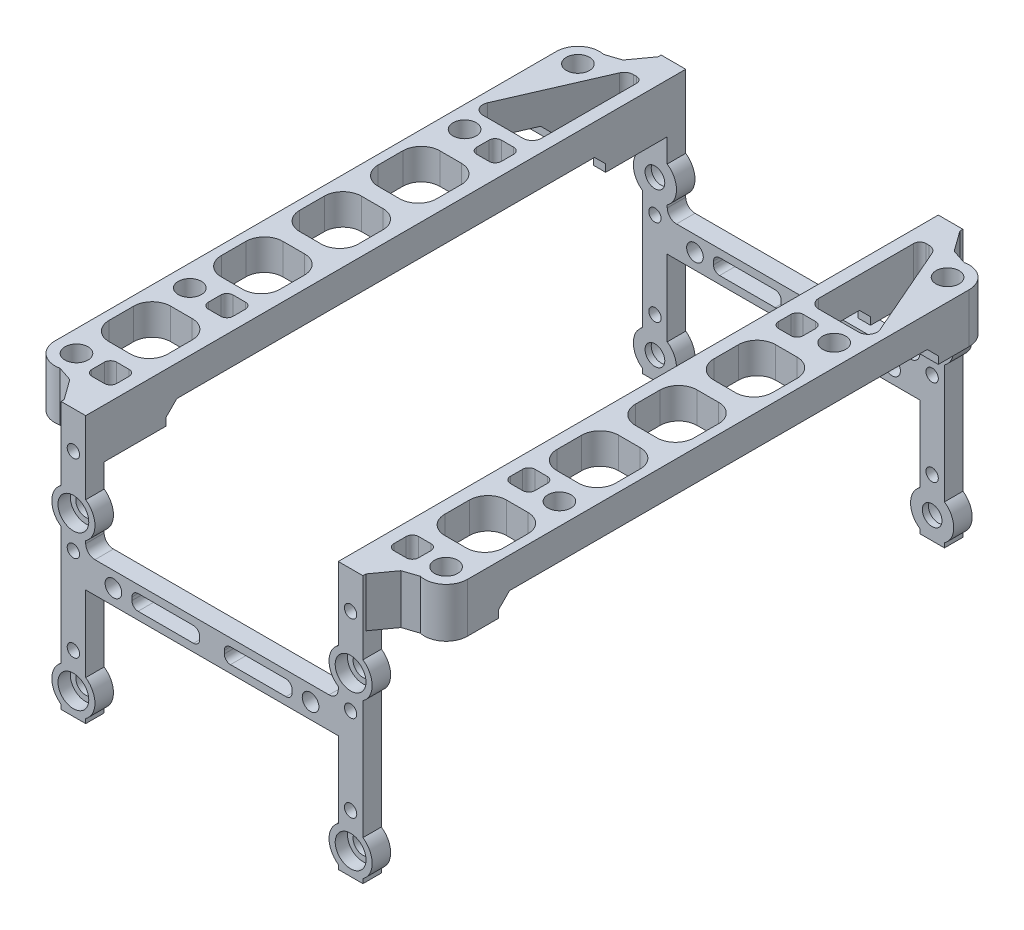
SolidWorks part; units mm, degrees
ref_plane "Front Plane" through (0, 0, 0) normal (0, 0, 1) x (1, 0, 0)
ref_plane "Top Plane" through (0, 0, 0) normal (0, 1, 0) x (1, 0, 0)
ref_plane "Right Plane" through (0, 0, 0) normal (1, 0, 0) x (0, 0, -1)
sketch "Sketch1" plane through (0, 0, 0) normal (1, 0, 0) x (0, 0, -1)
  line L0 (0, 0) -> (-3, 0)
  line L1 (0, 0) -> (91.4, 0) construction
  line L2 (0, 0) -> (0, 35.3)
  line L3 (0, 35.3) -> (91.4, 35.3) construction
  line L4 (91.4, 0) -> (91.4, 35.3)
  line L5 (-3, 0) -> (-3, 43.3)
  line L6 (-3, 43.3) -> (94.4, 43.3) construction
  line L7 (94.4, 43.3) -> (94.4, 0)
  line L8 (94.4, 0) -> (91.4, 0)
  line L9 (45.7, 43.3) -> (45.7, 35.3)
  line L10 (94.4, 43.3) -> (45.7, 43.3)
  line L11 (91.4, 35.3) -> (45.7, 35.3)
  dimension "D1" = 91.4
  dimension "D2" = 35.3
  dimension "D3" = 3
  dimension "D4" = 8
extrude "Boss-Extrude1" add sketch "Sketch1" along normal blind 4 contours L11 L4 L8 L7 L10 L9
sketch "Sketch2" plane through (0, 0, -94.4) normal (0, 0, 1) x (1, 0, 0)
  line L0 (2, 43.3) -> (2, 0) construction
  line L1 (2, 43.3) -> (2, 35.3) construction
  line L4 (4, 43.3) -> (0, 43.3) construction
  line L5 (4, 35.3) -> (0, 35.3) construction
  line L6 (4, 35.3) -> (0, 35.3) construction
  line L7 (4, 0) -> (0, 0) construction
  circle A0 centre (2, 28.6) radius 1.6
  circle A1 centre (2, 3.6) radius 1.6
  circle A3 centre (2, 37.3) radius 1
  circle A4 centre (2, 23.3) radius 1
  circle A5 centre (2, 9.3) radius 1
  dimension "D1" = 3.2
  dimension "D5" = 2
  dimension "D6" = 2
  dimension "D2" = 25
  dimension "D3" = 6.7
  dimension "D4" = 2
  dimension "D7" = 12
  dimension "D8" = 14
extrude "Cut-Extrude1" cut sketch "Sketch2" along normal through all and the other way through all
sketch "Sketch3" plane through (0, 0, -94.4) normal (0, 0, -1) x (-1, 0, 0)
  line L0 (-2, 28.6) -> (43, 28.6) construction
  line L1 (20.5, 28.6) -> (0, 28.6) construction
  line L2 (6, 55.8) -> (20.5, 55.8) construction
  line L5 (20.5, 23.8) -> (20.5, 18.8)
  line L8 (-2, 3.6) -> (42.5, 3.6) construction
  line L9 (20.5, 21.3) -> (0, 21.3) construction
  line L11 (0, 55.8) -> (0, 50.8) construction
  line L12 (20.5, 50.8) -> (6, 50.8) construction
  line L13 (20.5, 55.8) -> (20.5, 50.8) construction
  line L14 (0, 55.8) -> (3, 55.8) construction
  line L15 (0, 53.3) -> (20.5, 53.3) construction
  line L16 (-4, 43.3) -> (-4, 55.8) construction
  line L17 (-4, 55.8) -> (0, 55.8) construction
  line L18 (-4, 43.3) -> (0, 43.3) construction
  line L19 (0, 43.3) -> (0, 50.8) construction
  line L20 (4.5, 53.3) -> (4.5, 21.3) construction
  line L21 (0, 23.8) -> (0, 18.8) construction
  line L22 (0, 43.3) -> (0, 0) construction
  line L23 (-4, 43.3) -> (0, 43.3) construction
  line L24 (-4, 43.3) -> (-4, 0) construction
  line L25 (3, 50.8) -> (0, 50.8) construction
  line L26 (0, 23.8) -> (20.5, 23.8)
  line L27 (20.5, 18.8) -> (0, 18.8)
  line L28 (-4, 43.3) -> (-4, 31.4723) construction
  line L29 (-4, 18.8) -> (0, 18.8)
  line L30 (0, 43.3) -> (0, 35.3)
  line L31 (0, 25.7277) -> (0, 23.8)
  line L32 (-4, 25.7277) -> (-4, 18.8)
  line L34 (8.5, 22.55) -> (17.5, 22.55)
  line L35 (7.5, 21.55) -> (7.5, 21.05)
  line L36 (8.5, 20.05) -> (17.5, 20.05)
  line L37 (18.5, 21.55) -> (18.5, 21.05)
  line L38 (0, 35.3) -> (20.5, 23.8)
  line L39 (-4, 35.3) -> (0, 35.3) construction
  circle A0 centre (4.5, 53.3) radius 1.35 construction
  circle A1 centre (4.5, 21.3) radius 1.35
  arc A3 (6, 55.8) -> (3, 55.8) centre (4.5, 53.3) ccw construction
  circle A4 centre (-2, 28.6) radius 2.5
  arc A5 (3, 50.8) -> (6, 50.8) centre (4.5, 53.3) ccw construction
  circle A7 centre (-2, 28.6) radius 3.5
  arc A8 (17.5, 22.55) -> (18.5, 21.55) centre (17.5, 21.55) cw
  arc A9 (18.5, 21.05) -> (17.5, 20.05) centre (17.5, 21.05) cw
  arc A10 (8.5, 20.05) -> (7.5, 21.05) centre (8.5, 21.05) cw
  arc A11 (7.5, 21.55) -> (8.5, 22.55) centre (8.5, 21.55) cw
  circle A12 centre (-2, 28.6) radius 1.6 construction
  circle A13 centre (-2, 28.6) radius 1.6 construction
  circle A14 centre (-2, 20.8) radius 1 construction
  point P52 (18.5, 22.55)
  point P53 (18.5, 20.05)
  line M31 (0, 43.3) -> (-4, 43.3)
  line M32 (0, 0) -> (0, 43.3)
  line M33 (-4, 43.3) -> (-4, 0)
  dimension "D5" = 2.7
  dimension "D7" = 2
  dimension "D8" = 5
  dimension "D9" = 7
  dimension "D12" = 1
  dimension "D13" = 2
  dimension "D1" = 45
  dimension "D2" = 5
  dimension "D3" = 2.5
  dimension "D4" = 32
  dimension "D6" = 16
  dimension "D10" = 3
  dimension "D11" = 22
extrude "Boss-Extrude2" add sketch "Sketch3" against normal up to surface (3 mm away) contours L25 A5 L12 L13 L2 A3 L14 L17 L16 L19 A0 M31 | A7 A4 M32 | A7 A4 M33 M32 | A7 A4 M33 | A7 A4 M32 M33 | A7 L29 M33 M32 | L27 L5 L26 A1 L35 A11 L34 A8 L37 A9 L36 A10 M32
sketch "Sketch4" plane through (0, 0, -94.4) normal (0, 0, -1) x (-1, 0, 0)
  line L0 (20.5, 18.8) -> (20.5, -0.3) construction
  line L1 (-2, 3.6) -> (20.5, 3.6) construction
  circle A0 centre (-2, 3.6) radius 1.35
  circle A1 centre (-2, 3.6) radius 2.5
  point P8 (0, 0)
  point P10 (0, 0)
  point P11 (0, 0)
sketch "Sketch5" plane through (0, 43.3, 0) normal (0, 1, 0) x (1, 0, 0)
  line L0 (4, 45.7) -> (0, 45.7) construction
  line L1 (2, 45.7) -> (2, 91.4) construction
  line L3 (4, 91.4) -> (8.7463, 89.8179)
  line L4 (13, 86.4) -> (13, 45.7)
  line L5 (9.5, 91.4) -> (9.5, 45.6) construction
  line L8 (4, 91.4) -> (13, 88.4) construction
  line L9 (13, 88.4) -> (13, 45.7) construction
  line L10 (13, 45.7) -> (0, 45.7)
  line L11 (0, 45.7) -> (0, 91.4)
  line L12 (0, 91.4) -> (4, 91.4)
  line L13 (4, 94.4) -> (4, 45.7) construction
  line L14 (0, 94.4) -> (0, 45.7) construction
  line L15 (4, 94.4) -> (4, 45.7) construction
  line L16 (-0.5, 91.4) -> (0, 91.4) construction
  circle A0 centre (9.5, 86.4) radius 1.875 construction
  arc A2 (13, 86.4) -> (8.7463, 89.8179) centre (9.5, 86.4) ccw
  circle A3 centre (4, 78.4) radius 3.5 construction
  circle A4 centre (4, 69.4) radius 3.5 construction
  circle A5 centre (4, 60.4) radius 3.5 construction
  point P8 (0, 0)
  point P13 (0, 0)
  dimension "D1" = 3.75
  dimension "D6" = 3.5
  dimension "D7" = 7
  dimension "D2" = 5
  dimension "D4" = 3.5
  dimension "D5" = 2
  dimension "D8" = 8
  dimension "D10" = 9
  dimension "D9" = 3
extrude "Boss-Extrude3" add sketch "Sketch5" against normal up to surface (8 mm away) up to face at (2, 35.3, -68.55)
sketch "Sketch9" plane through (0, 0, -94.4) normal (0, 0, -1) x (-1, 0, 0)
  circle A2 centre (4.5, 21.3) radius 1.35
  circle A3 centre (4.5, 21.3) radius 2.5
  circle A4 centre (-2, 28.6) radius 1.35
  circle A5 centre (-2, 28.6) radius 3.5
  circle A6 centre (-2, 3.6) radius 1.35 construction
  circle A7 centre (-2, 3.6) radius 1.35
  circle A8 centre (-2, 3.6) radius 2.7378
  circle A12 centre (4.5, 21.3) radius 1.35 construction
  dimension "D1" = 7
extrude "Boss-Extrude4" [suppressed] add sketch "Sketch9" along normal blind 2
sketch "Sketch10" plane through (0, 0, -94.4) normal (0, 0, -1) x (-1, 0, 0)
  circle A0 centre (-2, 28.6) radius 1.6
  circle A1 centre (-2, 28.6) radius 3.5
  circle A2 centre (-2, 3.6) radius 1.6
  circle A3 centre (-2, 3.6) radius 3.5
  circle A4 centre (-2, 3.6) radius 1.6 construction
  circle A5 centre (-2, 28.6) radius 1.6 construction
  dimension "D1" = 7
extrude "Boss-Extrude5" add sketch "Sketch10" against normal up to surface (3 mm away) up to face at (-0.25, 28.6, -91.4)
sketch "Sketch11" plane through (0, 0, -94.4) normal (0, 0, -1) x (-1, 0, 0)
  circle A0 centre (-2, 28.6) radius 2.5
  circle A1 centre (-2, 3.6) radius 2.5
  circle A3 centre (-2, 28.6) radius 1.6 construction
  dimension "D1" = 5
extrude "Cut-Extrude4" cut sketch "Sketch11" against normal blind 2
ref_plane "Plane1" through (-20.5, 0, 0) normal (-1, 0, 0) x (0, 0, 1)
mirror "Mirror4" about plane through (-20.5, 0, 0) normal (-1, 0, 0) of bodies 115 108
mirror "Mirror5" about plane through (4, 0, -45.7) normal (0, 0, -1) of bodies 109
sketch "Sketch8" plane through (0, 43.3, 0) normal (0, 1, 0) x (1, 0, 0)
  line L0 (6.5, 34.4749) -> (6.5, 59.4749) construction
  line L1 (5, 50.2415) -> (8.5, 50.2415)
  line L2 (9.5, 86.4) -> (9.5, 5) construction
  line L3 (5, 62.9749) -> (8.5, 62.9749)
  line L6 (2, 88.4) -> (2, 72.9749)
  line L7 (3.5, 71.4749) -> (10, 71.4749)
  line L8 (11.3752, 73.5739) -> (4.8752, 88.4989)
  line L9 (3.5, 89.4) -> (3, 89.4)
  line L10 (0, 94.4) -> (0, -3) construction
  line L11 (2, 59.9749) -> (2, 55.9749)
  line L12 (13, 5) -> (13, 86.4) construction
  line L14 (5, 52.9749) -> (8.5, 52.9749)
  line L15 (11.5, 59.9749) -> (11.5, 55.9749)
  line L16 (3, 69.4749) -> (5, 69.4749)
  line L17 (2, 68.4749) -> (2, 66.4749)
  line L18 (3, 65.4749) -> (5, 65.4749)
  line L19 (6, 68.4749) -> (6, 66.4749)
  line L20 (2, 47.2415) -> (2, 43.2415)
  line L21 (5, 40.2415) -> (8.5, 40.2415)
  line L22 (11.5, 47.2415) -> (11.5, 43.2415)
  line L23 (6.5, 21.7415) -> (6.5, 46.7415) construction
  line L24 (5, 37.508) -> (8.5, 37.508)
  line L25 (2, 34.508) -> (2, 30.508)
  line L26 (5, 27.508) -> (8.5, 27.508)
  line L27 (11.5, 34.508) -> (11.5, 30.508)
  line L28 (6.5, 9.008) -> (6.5, 34.008) construction
  line L29 (9.5, 45.7) -> (-6.9785, 45.7) construction
  line L30 (6, 22.9251) -> (6, 24.9251)
  line L31 (3, 25.9251) -> (5, 25.9251)
  line L32 (2, 22.9251) -> (2, 24.9251)
  line L33 (3, 21.9251) -> (5, 21.9251)
  line L34 (9.5, 23.4) -> (-1.2891, 23.4) construction
  line L35 (11.5, 12.292) -> (11.5, 16.292)
  line L36 (5, 19.292) -> (8.5, 19.292)
  line L37 (2, 12.292) -> (2, 16.292)
  line L38 (5, 9.292) -> (8.5, 9.292)
  line L39 (-41, 91.4) -> (0, 91.4) construction
  line L40 (-20.5, 91.4) -> (-20.5, 40.2665) construction
  line L41 (-50.5, 23.4) -> (-39.7109, 23.4) construction
  line L42 (-50.5, 45.7) -> (-34.0215, 45.7) construction
  line L43 (-47.5, 9.008) -> (-47.5, 34.008) construction
  line L44 (-47.5, 21.7415) -> (-47.5, 46.7415) construction
  line L45 (-50.5, 86.4) -> (-50.5, 5) construction
  line L46 (-47.5, 34.4749) -> (-47.5, 59.4749) construction
  line L47 (-46, 9.292) -> (-49.5, 9.292)
  line L48 (-43, 12.292) -> (-43, 16.292)
  line L49 (-46, 19.292) -> (-49.5, 19.292)
  line L50 (-52.5, 12.292) -> (-52.5, 16.292)
  line L51 (-44, 21.9251) -> (-46, 21.9251)
  line L52 (-43, 22.9251) -> (-43, 24.9251)
  line L53 (-44, 25.9251) -> (-46, 25.9251)
  line L54 (-47, 22.9251) -> (-47, 24.9251)
  line L55 (-52.5, 34.508) -> (-52.5, 30.508)
  line L56 (-46, 27.508) -> (-49.5, 27.508)
  line L57 (-43, 34.508) -> (-43, 30.508)
  line L58 (-46, 37.508) -> (-49.5, 37.508)
  line L59 (-52.5, 47.2415) -> (-52.5, 43.2415)
  line L60 (-46, 40.2415) -> (-49.5, 40.2415)
  line L61 (-43, 47.2415) -> (-43, 43.2415)
  line L62 (-47, 68.4749) -> (-47, 66.4749)
  line L63 (-44, 65.4749) -> (-46, 65.4749)
  line L64 (-43, 68.4749) -> (-43, 66.4749)
  line L65 (-44, 69.4749) -> (-46, 69.4749)
  line L66 (-52.5, 59.9749) -> (-52.5, 55.9749)
  line L67 (-46, 52.9749) -> (-49.5, 52.9749)
  line L68 (-43, 59.9749) -> (-43, 55.9749)
  line L69 (-44.5, 89.4) -> (-44, 89.4)
  line L70 (-52.3752, 73.5739) -> (-45.8752, 88.4989)
  line L71 (-44.5, 71.4749) -> (-51, 71.4749)
  line L72 (-43, 88.4) -> (-43, 72.9749)
  line L73 (-46, 62.9749) -> (-49.5, 62.9749)
  line L74 (-46, 50.2415) -> (-49.5, 50.2415)
  line L75 (4, 91.4) -> (5.5, 91.4) construction
  line L76 (0, 94.4) -> (0, -3) construction
  line L78 (-41, 94.4) -> (-41, -3) construction
  line L79 (9.5, 23.4) -> (9.5, 5) construction
  line L80 (6, 3.9694) -> (6, 6.0306)
  line L81 (3, 7.0306) -> (5, 7.0306)
  line L82 (2, 4.0306) -> (2, 6.0306)
  line L83 (3, 3.0306) -> (5, 3.0306)
  line L84 (9.5, 5) -> (6, 5) construction
  line L85 (-44, 3.0306) -> (-46, 3.0306)
  line L86 (-43, 4.0306) -> (-43, 6.0306)
  line L87 (-44, 7.0306) -> (-46, 7.0306)
  line L88 (-47, 3.9694) -> (-47, 6.0306)
  line L89 (4, 94.4) -> (0, 94.4) construction
  arc A6 (10, 71.4749) -> (11.3752, 73.5739) centre (10, 72.9749) ccw
  arc A7 (2, 72.9749) -> (3.5, 71.4749) centre (3.5, 72.9749) ccw
  arc A8 (4.8752, 88.4989) -> (3.5, 89.4) centre (3.5, 87.9) ccw
  arc A9 (2, 88.4) -> (3, 89.4) centre (3, 88.4) cw
  arc A10 (13, 86.4) -> (8.7463, 89.8179) centre (9.5, 86.4) ccw construction
  arc A11 (13, 86.4) -> (8.7463, 89.8179) centre (9.5, 86.4) ccw construction
  circle A12 centre (9.5, 86.4) radius 1.875
  arc A13 (8.7463, 1.5821) -> (13, 5) centre (9.5, 5) ccw construction
  arc A14 (8.7463, 1.5821) -> (13, 5) centre (9.5, 5) ccw construction
  circle A15 centre (9.5, 5) radius 1.875
  circle A16 centre (9.5, 23.4) radius 1.875
  circle A17 centre (9.5, 68) radius 1.875
  arc A18 (5, 69.4749) -> (6, 68.4749) centre (5, 68.4749) cw
  arc A19 (6, 66.4749) -> (5, 65.4749) centre (5, 66.4749) cw
  arc A20 (3, 65.4749) -> (2, 66.4749) centre (3, 66.4749) cw
  arc A21 (2, 68.4749) -> (3, 69.4749) centre (3, 68.4749) cw
  arc A22 (8.5, 62.9749) -> (11.5, 59.9749) centre (8.5, 59.9749) cw
  arc A23 (11.5, 55.9749) -> (8.5, 52.9749) centre (8.5, 55.9749) cw
  arc A24 (5, 52.9749) -> (2, 55.9749) centre (5, 55.9749) cw
  arc A25 (2, 59.9749) -> (5, 62.9749) centre (5, 59.9749) cw
  arc A26 (8.5, 50.2415) -> (11.5, 47.2415) centre (8.5, 47.2415) cw
  arc A27 (2, 47.2415) -> (5, 50.2415) centre (5, 47.2415) cw
  arc A28 (5, 40.2415) -> (2, 43.2415) centre (5, 43.2415) cw
  arc A29 (11.5, 43.2415) -> (8.5, 40.2415) centre (8.5, 43.2415) cw
  arc A30 (8.5, 37.508) -> (11.5, 34.508) centre (8.5, 34.508) cw
  arc A31 (2, 34.508) -> (5, 37.508) centre (5, 34.508) cw
  arc A32 (5, 27.508) -> (2, 30.508) centre (5, 30.508) cw
  arc A33 (11.5, 30.508) -> (8.5, 27.508) centre (8.5, 30.508) cw
  arc A34 (2, 22.9251) -> (3, 21.9251) centre (3, 22.9251) ccw
  arc A35 (3, 25.9251) -> (2, 24.9251) centre (3, 24.9251) ccw
  arc A36 (6, 24.9251) -> (5, 25.9251) centre (5, 24.9251) ccw
  arc A37 (5, 21.9251) -> (6, 22.9251) centre (5, 22.9251) ccw
  arc A38 (11.5, 16.292) -> (8.5, 19.292) centre (8.5, 16.292) ccw
  arc A39 (5, 19.292) -> (2, 16.292) centre (5, 16.292) ccw
  arc A40 (2, 12.292) -> (5, 9.292) centre (5, 12.292) ccw
  arc A41 (8.5, 9.292) -> (11.5, 12.292) centre (8.5, 12.292) ccw
  arc A42 (-49.7463, 1.5821) -> (-54, 5) centre (-50.5, 5) cw construction
  arc A43 (-54, 86.4) -> (-49.7463, 89.8179) centre (-50.5, 86.4) cw construction
  arc A44 (-49.5, 9.292) -> (-52.5, 12.292) centre (-49.5, 12.292) cw
  arc A45 (-43, 12.292) -> (-46, 9.292) centre (-46, 12.292) cw
  arc A46 (-46, 19.292) -> (-43, 16.292) centre (-46, 16.292) cw
  arc A47 (-52.5, 16.292) -> (-49.5, 19.292) centre (-49.5, 16.292) cw
  arc A48 (-46, 21.9251) -> (-47, 22.9251) centre (-46, 22.9251) cw
  arc A49 (-47, 24.9251) -> (-46, 25.9251) centre (-46, 24.9251) cw
  arc A50 (-44, 25.9251) -> (-43, 24.9251) centre (-44, 24.9251) cw
  arc A51 (-43, 22.9251) -> (-44, 21.9251) centre (-44, 22.9251) cw
  arc A52 (-52.5, 30.508) -> (-49.5, 27.508) centre (-49.5, 30.508) ccw
  arc A53 (-46, 27.508) -> (-43, 30.508) centre (-46, 30.508) ccw
  arc A54 (-43, 34.508) -> (-46, 37.508) centre (-46, 34.508) ccw
  arc A55 (-49.5, 37.508) -> (-52.5, 34.508) centre (-49.5, 34.508) ccw
  arc A56 (-52.5, 43.2415) -> (-49.5, 40.2415) centre (-49.5, 43.2415) ccw
  arc A57 (-46, 40.2415) -> (-43, 43.2415) centre (-46, 43.2415) ccw
  arc A58 (-43, 47.2415) -> (-46, 50.2415) centre (-46, 47.2415) ccw
  arc A59 (-49.5, 50.2415) -> (-52.5, 47.2415) centre (-49.5, 47.2415) ccw
  arc A60 (-43, 59.9749) -> (-46, 62.9749) centre (-46, 59.9749) ccw
  arc A61 (-46, 52.9749) -> (-43, 55.9749) centre (-46, 55.9749) ccw
  arc A62 (-52.5, 55.9749) -> (-49.5, 52.9749) centre (-49.5, 55.9749) ccw
  arc A63 (-49.5, 62.9749) -> (-52.5, 59.9749) centre (-49.5, 59.9749) ccw
  arc A64 (-43, 68.4749) -> (-44, 69.4749) centre (-44, 68.4749) ccw
  arc A65 (-44, 65.4749) -> (-43, 66.4749) centre (-44, 66.4749) ccw
  arc A66 (-47, 66.4749) -> (-46, 65.4749) centre (-46, 66.4749) ccw
  arc A67 (-46, 69.4749) -> (-47, 68.4749) centre (-46, 68.4749) ccw
  circle A68 centre (-50.5, 68) radius 1.875
  circle A69 centre (-50.5, 23.4) radius 1.875
  circle A70 centre (-50.5, 5) radius 1.875
  circle A71 centre (-50.5, 86.4) radius 1.875
  arc A72 (-43, 88.4) -> (-44, 89.4) centre (-44, 88.4) ccw
  arc A73 (-45.8752, 88.4989) -> (-44.5, 89.4) centre (-44.5, 87.9) cw
  arc A74 (-43, 72.9749) -> (-44.5, 71.4749) centre (-44.5, 72.9749) cw
  arc A75 (-51, 71.4749) -> (-52.3752, 73.5739) centre (-51, 72.9749) cw
  arc A76 (2, 4.0306) -> (3, 3.0306) centre (3, 4.0306) ccw
  arc A77 (3, 7.0306) -> (2, 6.0306) centre (3, 6.0306) ccw
  arc A78 (6, 6.0306) -> (5, 7.0306) centre (5, 6.0306) ccw
  arc A79 (5, 3.0306) -> (6, 3.9694) centre (5.0019, 4.0306) ccw
  arc A80 (-46, 3.0306) -> (-47, 3.9694) centre (-46.0019, 4.0306) cw
  arc A81 (-47, 6.0306) -> (-46, 7.0306) centre (-46, 6.0306) cw
  arc A82 (-44, 7.0306) -> (-43, 6.0306) centre (-44, 6.0306) cw
  arc A83 (-43, 4.0306) -> (-44, 3.0306) centre (-44, 4.0306) cw
  dimension "D5" = 1.5
  dimension "D6" = 1
  dimension "D7" = 3.75
  dimension "D8" = 3.75
  dimension "D16" = 63
  dimension "D17" = 63
  dimension "D4" = 1
  dimension "D22" = 3
  dimension "D2" = 25
  dimension "D9" = 0.5
  dimension "D10" = 3
  dimension "D11" = 2
  dimension "D12" = 3.5
  dimension "D13" = 12
  dimension "D14" = 6
  dimension "D15" = 6.5
  dimension "D18" = 2
  dimension "D19" = 4
  dimension "D3" = 5
  dimension "D20" = 1.5
  dimension "D21" = 2.5
  dimension "D24" = 10
  dimension "D23" = 3
extrude "Cut-Extrude3" cut sketch "Sketch8" against normal through all
chamfer "Chamfer1" distance 2.5 4 edges at (-45, 39.3, 0) (-45, 39.3, -91.4) (4, 39.3, 0) (4, 39.3, -91.4)
sketch "Sketch12" plane through (0, 35.3, 0) normal (0, -1, 0) x (1, 0, 0)
  line L0 (0, 0) -> (-41, 0) construction
  line L1 (-20.5, 0) -> (-20.5, -83.4352) construction
  line L2 (0, -45.7) -> (-20.5, -45.7) construction
  line L3 (0, -91.4) -> (0, 0) construction
  circle A0 centre (9.5, -5) radius 3
  circle A1 centre (9.5, -23.4) radius 3
  circle A2 centre (9.5, -86.4) radius 3
  circle A3 centre (9.5, -68) radius 3
  circle A4 centre (-50.5, -86.4) radius 3
  circle A5 centre (-50.5, -68) radius 3
  circle A6 centre (-50.5, -23.4) radius 3
  circle A7 centre (-50.5, -5) radius 3
  dimension "D1" = 6
extrude "Cut-Extrude7" cut sketch "Sketch12" against normal blind 4.5
sketch "Sketch13" plane through (-54, 0, 0) normal (-1, 0, 0) x (0, 0, 1)
  line L0 (-45.7, 38.3) -> (-45.7, 43.3) construction
  line L1 (-81.4, 38.3) -> (-10, 38.3)
  line L2 (-81.4, 38.3) -> (-81.4, 30.9146)
  line L3 (-81.4, 30.9146) -> (-10, 30.9146)
  line L4 (-10, 38.3) -> (-10, 30.9146)
  line L5 (-5, 43.3) -> (-86.4, 43.3) construction
  line L6 (-5, 35.3) -> (-5, 43.3) construction
  line L7 (-5, 35.3) -> (-86.4, 35.3) construction
  dimension "D1" = 5
  dimension "D2" = 3
extrude "Cut-Extrude8" cut sketch "Sketch13" against normal through all
chamfer "Chamfer4" distance 1.8 angle 45 8 edges at (11.7178, 38.3, -10) (1.5322, 38.3, -10) (10.4834, 38.3, -81.4) (1, 38.3, -81.4) (-42.5322, 38.3, -10) (-52.7178, 38.3, -10) (-42, 38.3, -81.4) (-51.4834, 38.3, -81.4)
fillet "Fillet1" radius 1.5 4 edges at (-41, 23.8, -92.9) (0, 23.8, -92.9) (0, 23.8, 1.5) (-41, 23.8, 1.5)
